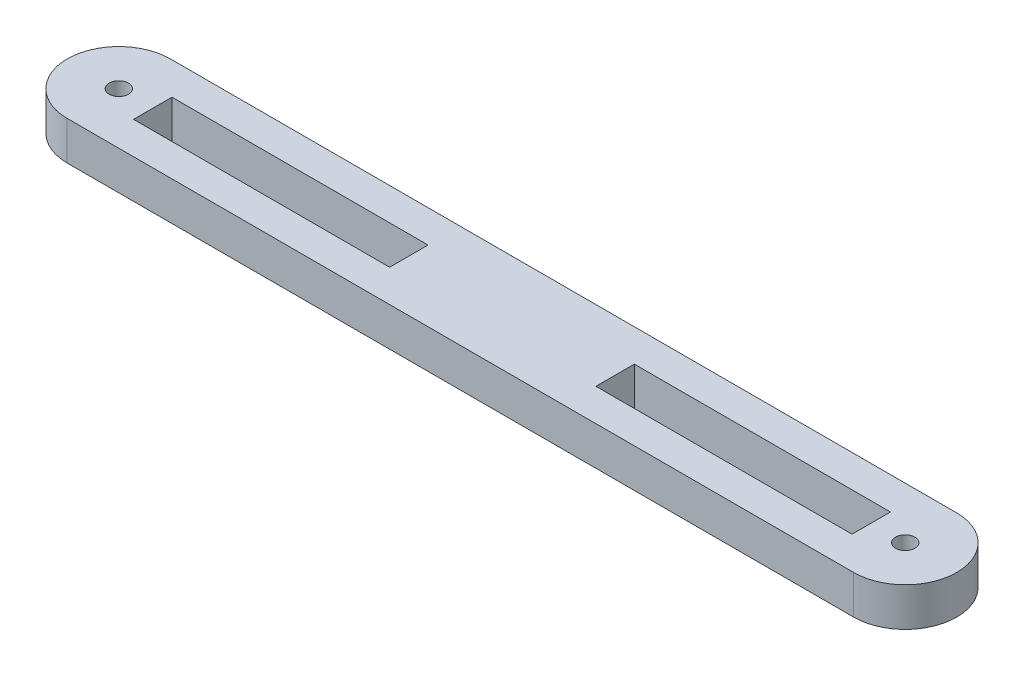
SolidWorks part; units mm, degrees
ref_plane "Front Plane" through (0, 0, 0) normal (0, 0, 1) x (1, 0, 0)
ref_plane "Top Plane" through (0, 0, 0) normal (0, 1, 0) x (1, 0, 0)
ref_plane "Right Plane" through (0, 0, 0) normal (1, 0, 0) x (0, 0, -1)
sketch "Sketch1" plane through (0, 0, 0) normal (0, 1, 0) x (1, 0, 0)
  line L0 (0, 0) -> (122, 0) construction
  line L1 (0, 0) -> (122, 0) construction
  line L2 (0, 8) -> (122, 8)
  line L3 (0, -8) -> (122, -8)
  circle A0 centre (0, 0) radius 1.5
  circle A1 centre (122, 0) radius 1.5
  arc A2 (0, 8) -> (0, -8) centre (0, 0) ccw
  arc A3 (122, -8) -> (122, 8) centre (122, 0) ccw
  point P5 (61, 0)
  dimension "D1" = 122
extrude "Boss-Extrude1" add sketch "Sketch1" along normal blind 6 contours A1 | L3 A3 L2 A2 | A0
sketch "Sketch2" plane through (0, 6, 0) normal (0, 1, 0) x (1, 0, 0)
  line L0 (0, 0) -> (122, 0) construction
  line L1 (61, 0) -> (61, 4.3922) construction
  line L2 (61, 0) -> (61, -4.2353) construction
  line L3 (61, -4.2353) -> (0, -4.2353) construction
  line L4 (30.5, -4.2353) -> (30.5, 0) construction
  line L5 (30.5, 0) -> (30.5, 4.3922) construction
  line L6 (30.5, 4.3922) -> (0, 4.3922) construction
  line L7 (15.25, 4.3922) -> (15.25, 0) construction
  line L8 (8.2936, 4.3922) -> (8.2936, 0) construction
  line L9 (105.9998, 2.9804) -> (77.0002, 2.9804)
  line L10 (16.0002, -2.9804) -> (44.9998, -2.9804)
  line L11 (16.0002, -2.9804) -> (16.0002, 2.9804)
  line L12 (16.0002, 2.9804) -> (44.9998, 2.9804)
  line L13 (44.9998, -2.9804) -> (44.9998, 2.9804)
  line L14 (16.0002, -2.9804) -> (44.9998, 2.9804) construction
  line L15 (16.0002, 2.9804) -> (44.9998, -2.9804) construction
  line L16 (16.0002, 2.9804) -> (5.2685, 2.9804)
  line L17 (16.0002, 2.9804) -> (16.0002, -2.9804)
  line L18 (16.0002, -2.9804) -> (5.2685, -2.9804)
  line L19 (5.2685, 2.9804) -> (5.2685, -2.9804)
  line L20 (77.0002, -2.9804) -> (77.0002, 2.9804)
  line L21 (105.9998, -2.9804) -> (77.0002, -2.9804)
  line L23 (105.9998, -2.9804) -> (116.7315, -2.9804)
  line L24 (116.7315, 2.9804) -> (116.7315, -2.9804)
  line L25 (105.9998, 2.9804) -> (116.7315, 2.9804)
extrude "Cut-Extrude1" cut sketch "Sketch2" against normal blind 14 contours L10 L13 L12 L11 | L16 L19 L18 L11 | L9 L20 L21 L23 L24 L25
